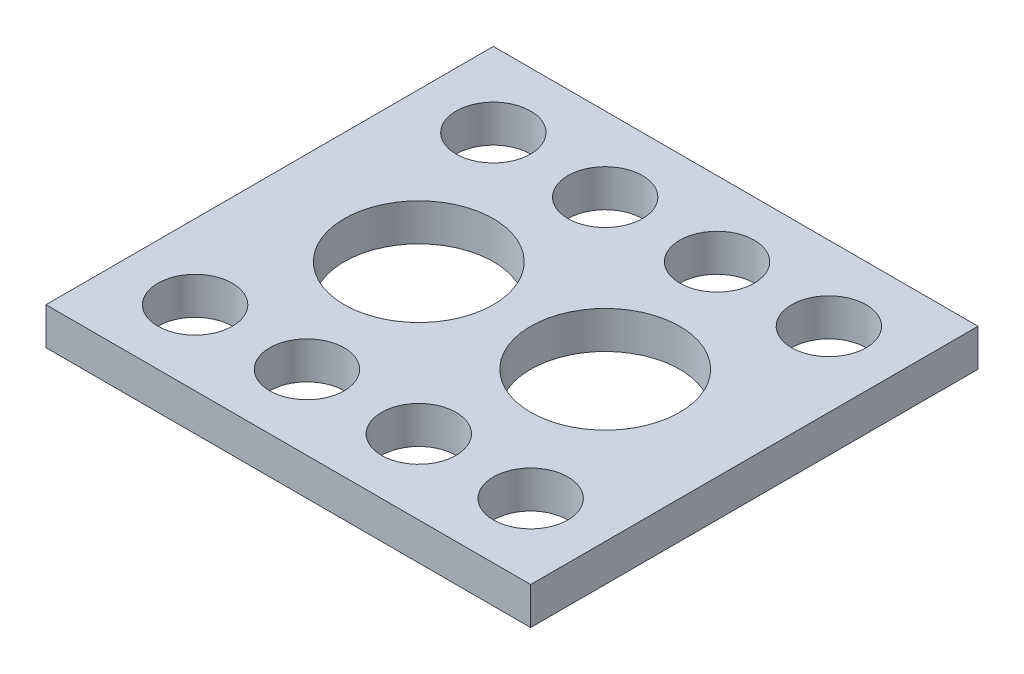
SolidWorks part; units mm, degrees
ref_plane "Front Plane" through (0, 0, 0) normal (0, 0, 1) x (1, 0, 0)
ref_plane "Top Plane" through (0, 0, 0) normal (0, 1, 0) x (1, 0, 0)
ref_plane "Right Plane" through (0, 0, 0) normal (1, 0, 0) x (0, 0, -1)
sketch "Sketch1" plane through (0, 0, 0) normal (0, 1, 0) x (1, 0, 0)
  line L1 (0, 0) -> (165.1, 0)
  line L2 (0, 0) -> (0, 152.4)
  line L3 (0, 152.4) -> (165.1, 152.4)
  line L4 (165.1, 0) -> (165.1, 152.4)
  circle A0 centre (25.4, 127) radius 12.7
  circle A1 centre (63.5, 127) radius 12.7
  circle A2 centre (101.6, 127) radius 12.7
  circle A3 centre (139.7, 127) radius 12.7
  circle A4 centre (25.4, 25.4) radius 12.7
  circle A5 centre (63.5, 25.4) radius 12.7
  circle A6 centre (101.6, 25.4) radius 12.7
  circle A7 centre (139.7, 25.4) radius 12.7
  circle A8 centre (50.8, 76.2) radius 25.4
  circle A9 centre (114.3, 76.2) radius 25.4
  point P25 (50.8, 127)
  point P26 (114.3, 127)
  point P27 (0, 0)
  point P28 (0, 0)
  dimension "D3" = 25.4
  dimension "D7" = 25.4
  dimension "D13" = 50.8
  dimension "D14" = 50.8
  dimension "D1" = 152.4
  dimension "D2" = 165.1
  dimension "D4" = 25.4
  dimension "D5" = 25.4
  dimension "D8" = 25.4
  dimension "D9" = 25.4
  dimension "D10" = 114.3
  dimension "D12" = 114.3
  dimension "D15" = 76.2
  dimension "D16" = 76.2
  dimension "D6" = 4
  dimension "D11" = 4
extrude "Boss-Extrude1" add sketch "Sketch1" along normal blind 12.7
